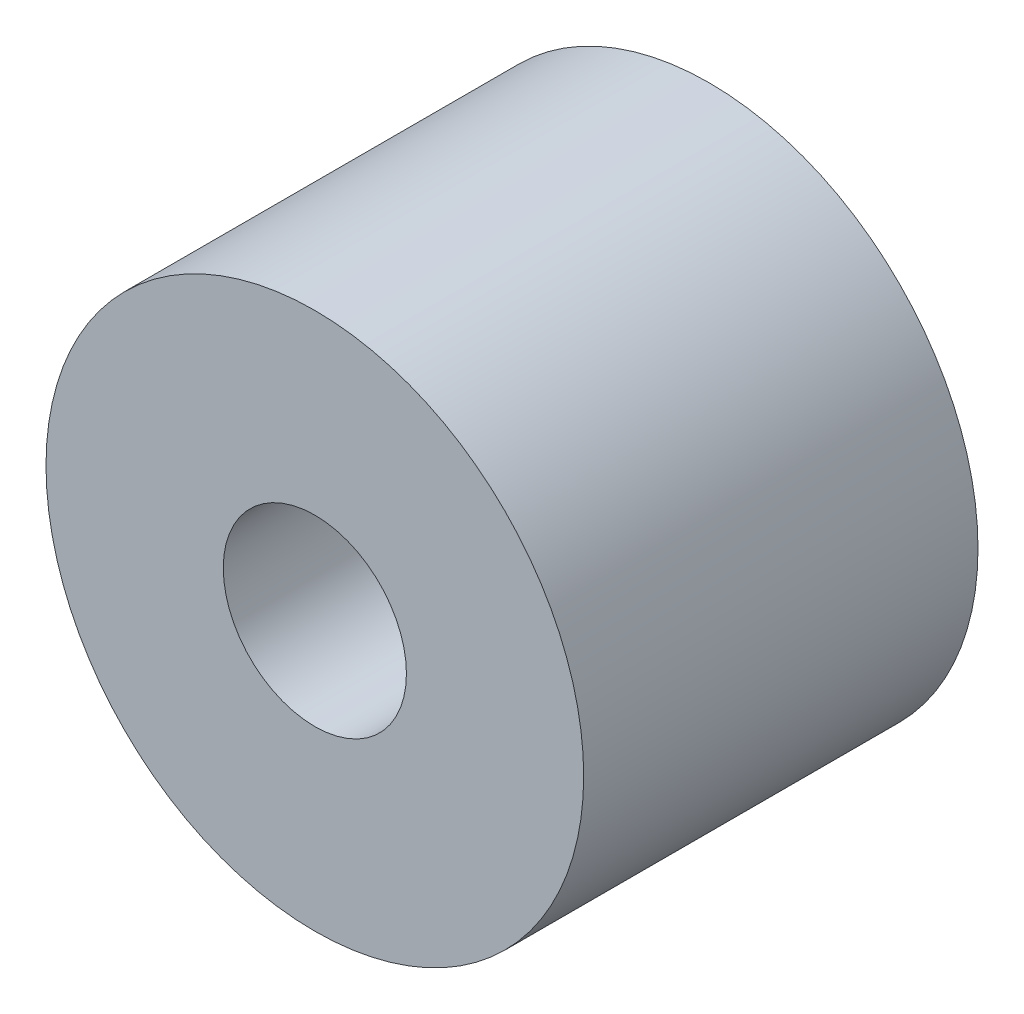
SolidWorks part; units mm, degrees
material "ABS"
ref_plane "Front Plane" through (0, 0, 0) normal (0, 0, 1) x (1, 0, 0)
ref_plane "Top Plane" through (0, 0, 0) normal (0, 1, 0) x (1, 0, 0)
ref_plane "Right Plane" through (0, 0, 0) normal (1, 0, 0) x (0, 0, -1)
sketch "Sketch1" plane through (0, 0, 0) normal (0, 0, 1) x (1, 0, 0)
  circle A0 centre (0, 0) radius 7.5
  circle A1 centre (0, 0) radius 2.555
  dimension "D1" = 15
  dimension "D2" = 5.11
extrude "Boss-Extrude1" add sketch "Sketch1" along normal blind 11
cosmetic thread "Cosmetic Thread1" parameters "D2"=6.35
